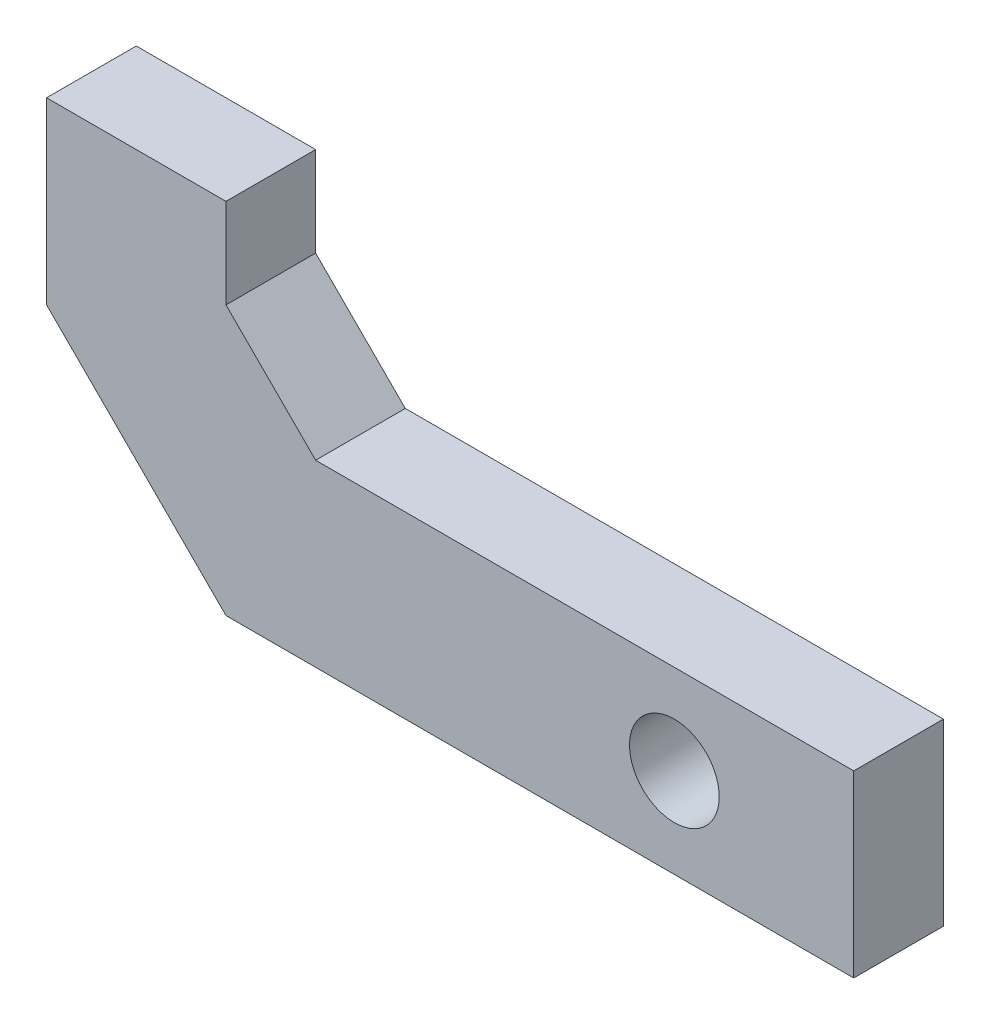
SolidWorks part; units mm, degrees
ref_plane "Front Plane" through (0, 0, 0) normal (0, 0, 1) x (1, 0, 0)
ref_plane "Top Plane" through (0, 0, 0) normal (0, 1, 0) x (1, 0, 0)
ref_plane "Right Plane" through (0, 0, 0) normal (1, 0, 0) x (0, 0, -1)
sketch "Sketch1" plane through (0, 0, 0) normal (0, 0, 1) x (1, 0, 0)
  line L0 (0, 0) -> (-5.08, 5.08)
  line L1 (-5.08, 5.08) -> (-5.08, 10.16)
  line L2 (-5.08, 10.16) -> (0, 10.16)
  line L3 (2.54, 5.08) -> (17.78, 5.08)
  line L4 (17.78, 5.08) -> (17.78, 0)
  line L5 (17.78, 0) -> (0, 0)
  line L6 (0, 10.16) -> (0, 7.62)
  line L7 (0, 7.62) -> (2.54, 5.08)
  dimension "D1" = 5.08
  dimension "D2" = 5.08
  dimension "D3" = 5.08
  dimension "D4" = 15.24
  dimension "D5" = 22.86
  dimension "D6" = 5.08
  dimension "D7" = 135
extrude "Boss-Extrude1" add sketch "Sketch1" along normal blind 2.54
sketch "Sketch2" plane through (0, 0, 2.54) normal (0, 0, 1) x (1, 0, 0)
  line L0 (17.78, 0) -> (17.78, 5.08) construction
  circle A0 centre (12.7, 2.54) radius 1.27
  point P4 (17.78, 2.54)
  dimension "D1" = 2.54
  dimension "D2" = 5.08
extrude "Cut-Extrude1" cut sketch "Sketch2" against normal up to next
